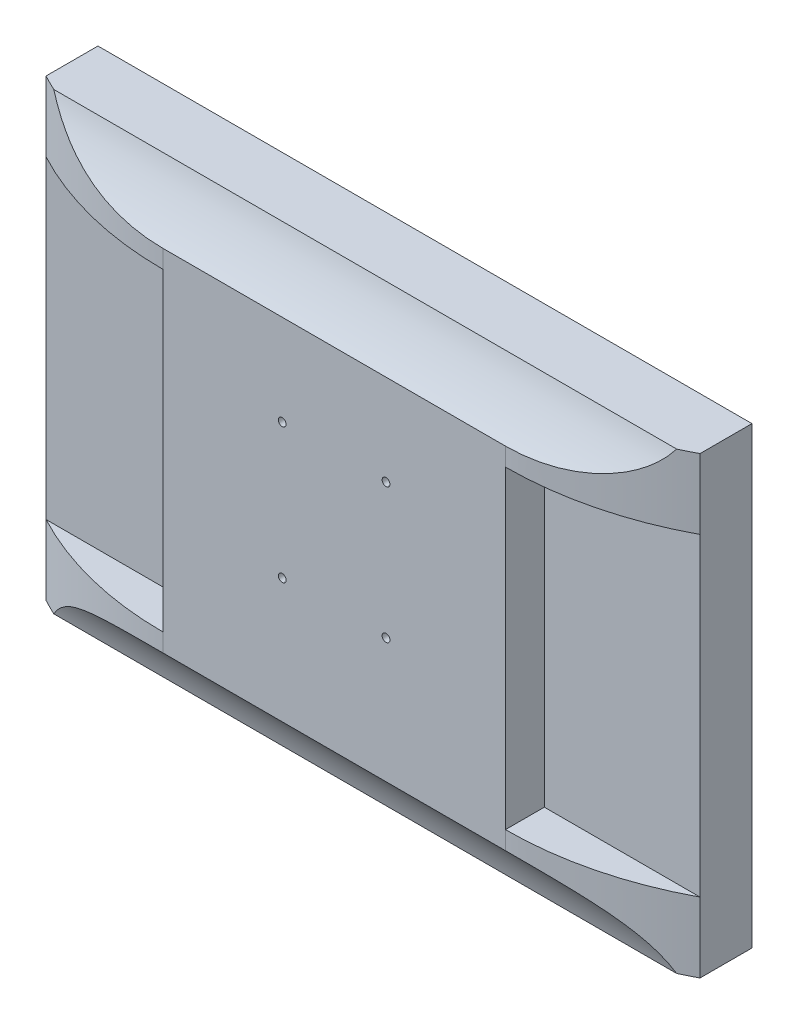
SolidWorks part; units mm, degrees
ref_plane "正面" through (0, 0, 0) normal (0, 0, 1) x (1, 0, 0)
ref_plane "平面" through (0, 0, 0) normal (0, 1, 0) x (1, 0, 0)
ref_plane "右側面" through (0, 0, 0) normal (1, 0, 0) x (0, 0, -1)
sketch "ｽｹｯﾁ1" plane through (0, 0, 0) normal (0, 0, 1) x (1, 0, 0)
  line L1 (-126, -87.5) -> (126, -87.5)
  line L2 (-126, -87.5) -> (-126, 87.5)
  line L3 (-126, 87.5) -> (126, 87.5)
  line L4 (126, -87.5) -> (126, 87.5)
  line L5 (-126, -87.5) -> (126, 87.5) construction
  line L6 (-126, 87.5) -> (126, -87.5) construction
  point P0 (0, 0)
  dimension "D1" = 175
  dimension "D2" = 252
extrude "ﾎﾞｽ - 押し出し1" add sketch "ｽｹｯﾁ1" along normal blind 20
sketch "ｽｹｯﾁ2" plane through (0, 0, 20) normal (0, 0, 1) x (1, 0, 0)
  line L0 (126, 87.5) -> (-126, 87.5) construction
  line L1 (-66, -62.5) -> (66, -62.5)
  line L2 (-66, -62.5) -> (-66, 62.5)
  line L3 (-66, 62.5) -> (66, 62.5)
  line L4 (66, -62.5) -> (66, 62.5)
  line L5 (-66, -62.5) -> (66, 62.5) construction
  line L6 (-66, 62.5) -> (66, -62.5) construction
  line L7 (-126, 87.5) -> (-126, -87.5) construction
  point P0 (0, 0)
  point P10 (-126, 0)
  dimension "D1" = 25
  dimension "D2" = 60
extrude "ﾎﾞｽ - 押し出し2" add sketch "ｽｹｯﾁ2" along normal blind 15
sketch "ｽｹｯﾁ4" plane through (0, 62.5, 0) normal (0, 1, 0) x (1, 0, 0)
  line L0 (66, -35) -> (-66, -35) construction
  line L1 (-66, -35) -> (-66, -20)
  line L2 (-66, -20) -> (-126, -20)
  arc A0 (-66, -35) -> (-126, -20) centre (-66, 92.5) cw
extrude "ﾎﾞｽ - 押し出し3" add sketch "ｽｹｯﾁ4" against normal up to surface (125 mm away) up to face at (0, -62.5, 27.5)
mirror "ﾐﾗｰ1" about plane through (0, 0, 0) normal (1, 0, 0) of "ﾎﾞｽ - 押し出し3"
sketch "ｽｹｯﾁ5" plane through (0, -62.5, 0) normal (0, -1, 0) x (1, 0, 0)
  line L2 (-126, 20) -> (126, 20)
  line L3 (66, 35) -> (-66, 35)
  line L4 (-126, 20) -> (126, 20)
  line L5 (66, 35) -> (-66, 35)
  arc A2 (126, 20) -> (66, 35) centre (66, -92.5) ccw
  arc A3 (-66, 35) -> (-126, 20) centre (-66, -92.5) ccw
  arc A4 (126, 20) -> (66, 35) centre (66, -92.5) ccw
  arc A5 (-66, 35) -> (-126, 20) centre (-66, -92.5) ccw
  dimension "D1" = 0
extrude "ﾎﾞｽ - 押し出し4" add sketch "ｽｹｯﾁ5" along normal up to surface (150 mm away)
mirror "ﾐﾗｰ2" about plane through (0, 0, 0) normal (0, 1, 0) of "ﾎﾞｽ - 押し出し4"
sketch "ｽｹｯﾁ6" plane through (0, 62.5, 0) normal (0, 1, 0) x (1, 0, 0)
  line L0 (66, -35) -> (-66, -35) construction
  line L1 (126, -20) -> (-126, -20) construction
  line L2 (66, -35) -> (-66, -35)
  line L3 (126, -20) -> (-126, -20)
  arc A0 (-126, -20) -> (-66, -35) centre (-66, 92.5) ccw construction
  arc A1 (66, -35) -> (126, -20) centre (66, 92.5) ccw construction
  arc A2 (-126, -20) -> (-66, -35) centre (-66, 92.5) ccw
  arc A3 (66, -35) -> (126, -20) centre (66, 92.5) ccw
extrude "ﾎﾞｽ - 押し出し5" add sketch "ｽｹｯﾁ6" along normal up to surface (25 mm away) up to face at (0, 87.5, 10)
sketch "ｽｹｯﾁ7" plane through (-126, 0, 0) normal (-1, 0, 0) x (0, 0, 1)
  line L0 (35, 87.5) -> (20, 87.5) construction
  line L1 (35, 87.5) -> (35, -87.5) construction
  line L2 (20, 87.5) -> (20, -87.5) construction
  line L3 (23, 87.5) -> (35, 87.5)
  line L4 (35, 87.5) -> (35, 67.5)
  arc A0 (23, 87.5) -> (35, 67.5) centre (71.7027, 103.1216) ccw
  dimension "D1" = 3
  dimension "D2" = 20
extrude "ｶｯﾄ - 押し出し1" cut sketch "ｽｹｯﾁ7" against normal through all contours L4 A0 L3
mirror "ﾐﾗｰ3" about plane through (0, 0, 0) normal (0, 1, 0) of "ｶｯﾄ - 押し出し1"
sketch "ｽｹｯﾁ8" plane through (0, 0, 35) normal (0, 0, 1) x (1, 0, 0)
  line L0 (120, 87.5) -> (-120, 87.5) construction
  line L1 (-126, 87.5) -> (-126, -87.5) construction
  circle A0 centre (-20, 32.5) radius 1.5
  circle A1 centre (20, 32.5) radius 1.5
  circle A2 centre (-20, -19.5) radius 1.5
  circle A3 centre (20, -19.5) radius 1.5
  dimension "D2" = 3
  dimension "D3" = 3
  dimension "D4" = 3
  dimension "D5" = 3
  dimension "D1" = 55
  dimension "D6" = 55
  dimension "D7" = 40
  dimension "D8" = 106
  dimension "D9" = 40
  dimension "D10" = 106
  dimension "D11" = 52
  dimension "D12" = 52
extrude "ｶｯﾄ - 押し出し2" cut sketch "ｽｹｯﾁ8" against normal blind 10
sketch "ｽｹｯﾁ10" plane through (-126, 0, 0) normal (-1, 0, 0) x (0, 0, 1)
  line L0 (20, 87.5) -> (0, 87.5) construction
  line L1 (40, 60.5) -> (20, 60.5)
  line L2 (40, 60.5) -> (40, -60.5)
  line L3 (40, -60.5) -> (20, -60.5)
  line L4 (20, 60.5) -> (20, -60.5)
  line L5 (40, 60.5) -> (20, -60.5) construction
  line L6 (40, -60.5) -> (20, 60.5) construction
  line L7 (20, -87.5) -> (0, -87.5) construction
  line L8 (20, 87.5) -> (20, -87.5) construction
  point P0 (30, 0)
  dimension "D1" = 27
  dimension "D2" = 27
  dimension "D3" = 0
  dimension "D4" = 20
extrude "ｶｯﾄ - 押し出し4" cut sketch "ｽｹｯﾁ10" against normal blind 60
mirror "ﾐﾗｰ4" about plane through (0, 0, 0) normal (1, 0, 0) of "ｶｯﾄ - 押し出し4"
sketch "ｽｹｯﾁ11" plane through (-66, 0, 0) normal (-1, 0, 0) x (0, 0, 1)
  line L0 (35, 60.5) -> (35, -60.5) construction
  line L1 (25, 37.5) -> (21, 37.5)
  line L2 (25, 37.5) -> (25, 27.5)
  line L3 (25, 27.5) -> (21, 27.5)
  line L4 (21, 37.5) -> (21, 27.5)
  line L5 (25, 37.5) -> (21, 27.5) construction
  line L6 (25, 27.5) -> (21, 37.5) construction
  line L7 (26, 22.5) -> (21, 22.5)
  line L8 (26, 22.5) -> (26, 5.5)
  line L9 (26, 5.5) -> (21, 5.5)
  line L10 (21, 22.5) -> (21, 5.5)
  line L11 (26, 22.5) -> (21, 5.5) construction
  line L12 (26, 5.5) -> (21, 22.5) construction
  line L13 (20, 87.5) -> (0, 87.5) construction
  point P0 (23, 32.5)
  point P5 (23.5, 14)
  dimension "D1" = 4
  dimension "D2" = 5
  dimension "D3" = 15
  dimension "D4" = 10
  dimension "D5" = 9
  dimension "D6" = 10
  dimension "D7" = 17
  dimension "D8" = 50
extrude "ｶｯﾄ - 押し出し5" cut sketch "ｽｹｯﾁ11" against normal blind 10
